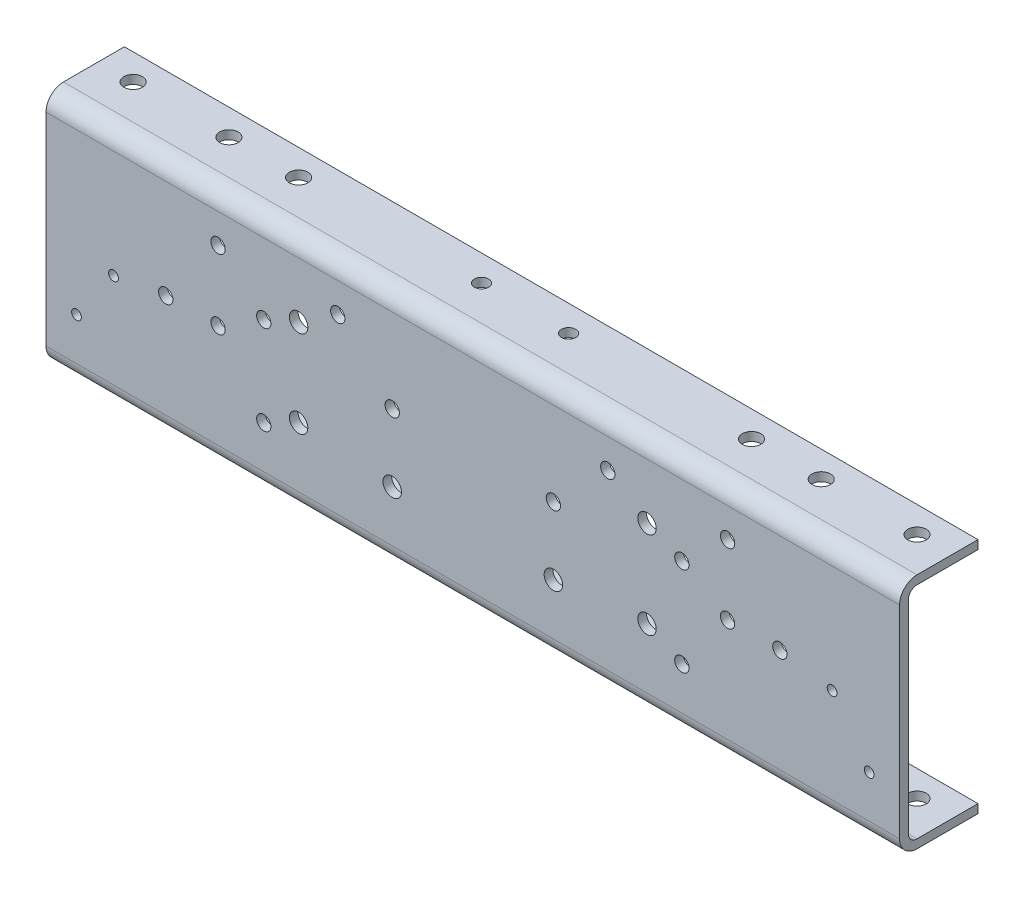
SolidWorks part; units mm, degrees
material "ASTM A36"
ref_plane "Front" through (0, 0, 0) normal (0, 0, 1) x (1, 0, 0)
ref_plane "Top" through (0, 0, 0) normal (0, 1, 0) x (1, 0, 0)
ref_plane "Side" through (0, 0, 0) normal (1, 0, 0) x (0, 0, -1)
sketch "Sketch1" plane through (0, 0, 0) normal (1, 0, 0) x (0, 0, -1)
  line L0 (57.15, 86.5188) -> (12.7, 86.5188)
  line L1 (0, 73.8188) -> (0, -73.8188)
  line L2 (12.7, -86.5187) -> (57.15, -86.5187)
  line L3 (57.15, -86.5187) -> (57.15, -80.1688)
  line L4 (57.15, -80.1688) -> (12.7, -80.1688)
  line L5 (6.35, -73.8188) -> (6.35, 73.8188)
  line L6 (12.7, 80.1688) -> (57.15, 80.1688)
  line L7 (57.15, 80.1688) -> (57.15, 86.5188)
  arc A0 (12.7, 86.5188) -> (0, 73.8188) centre (12.7, 73.8188) ccw
  arc A1 (0, -73.8188) -> (12.7, -86.5187) centre (12.7, -73.8188) ccw
  arc A2 (12.7, -80.1688) -> (6.35, -73.8188) centre (12.7, -73.8188) cw
  arc A3 (6.35, 73.8188) -> (12.7, 80.1688) centre (12.7, 73.8188) cw
  dimension "D4" = 6.35
  dimension "D1" = 6.35
  dimension "D2" = 57.15
  dimension "D3" = 173.0375
extrude "Extrude1" add sketch "Sketch1" along normal mid plane 622.3
sketch "Sketch2" plane through (0, 0, 0) normal (0, 0, 1) x (1, 0, 0)
  line L0 (0, 62.5223) -> (0, -87.3125) construction
  line L1 (58.7375, -36.5125) -> (58.7375, 12.7) construction
  line L5 (127, -30.1625) -> (127, 33.3375) construction
  line L11 (152.4, -42.8625) -> (152.4, 22.225) construction
  line L12 (288.925, -42.8625) -> (152.4, -42.8625) construction
  line L17 (185.7375, 1.5875) -> (185.7375, 52.3875) construction
  line L18 (185.7375, 52.3875) -> (98.425, 52.3875) construction
  line L20 (50, 0) -> (-50, 0) construction
  line L25 (0, -50) -> (0, 50) construction
  circle A0 centre (-152.4, 22.225) radius 5.207
  circle A1 centre (-185.7375, 52.3875) radius 5.207
  circle A2 centre (-223.8375, 1.5875) radius 5.207
  circle A3 centre (-261.9375, -4.7625) radius 3.556
  circle A4 centre (-288.925, -42.8625) radius 3.556
  circle A5 centre (-152.4, -42.8625) radius 5.207
  circle A6 centre (-127, -30.1625) radius 6.731
  circle A7 centre (-127, 33.3375) radius 6.731
  circle A8 centre (-98.425, 52.3875) radius 5.207
  circle A9 centre (-58.7375, 12.7) radius 5.207
  circle A10 centre (-58.7375, -36.5125) radius 6.731
  circle A11 centre (-185.7375, 1.5875) radius 5.207
  circle A36 centre (98.425, 52.3875) radius 5.207
  circle A37 centre (127, 33.3375) radius 6.731
  circle A38 centre (152.4, 22.225) radius 5.207
  circle A39 centre (185.7375, 52.3875) radius 5.207
  circle A40 centre (223.8375, 1.5875) radius 5.207
  circle A41 centre (185.7375, 1.5875) radius 5.207
  circle A42 centre (261.9375, -4.7625) radius 3.556
  circle A43 centre (288.925, -42.8625) radius 3.556
  circle A44 centre (152.4, -42.8625) radius 5.207
  circle A45 centre (127, -30.1625) radius 6.731
  circle A46 centre (58.7375, 12.7) radius 5.207
  circle A47 centre (58.7375, -36.5125) radius 6.731
  point P3 (0, -87.3125)
other "AlignGroup4" parameters "D25"=7.112, "D26"=10.414, "D27"=13.462, "D30"=7.112, "D17"=13.462, "D18"=10.414, "D19"=7.112, "D20"=10.414, "D21"=7.112, "D14"=10.414, "D15"=7.112, "D22"=13.462, "D23"=13.462, "D24"=13.462, "D1"=0, "D2"=61.9125, "D3"=52.3875, "D4"=12.7, "D5"=1.5875, "D6"=12.7, "D7"=52.3875, "D8"=0, "D9"=58.7375, "D10"=98.425, "D11"=127, "D12"=152.4, "D13"=185.7375, "D16"=288.925, "D28"=36.5125, "D29"=12.7, "D31"=31.75, "D32"=88.9, "D33"=139.7
extrude "Cut-Web Holes" cut sketch "Sketch2" against normal through all
sketch "Sketch3" plane through (0, 0, 0) normal (0, 1, 0) x (1, 0, 0)
  line L0 (-165.1, 38.1) -> (-31.75, 38.1) construction
  line L1 (-31.75, 38.1) -> (31.75, 38.1) construction
  line L2 (31.75, 38.1) -> (165.1, 38.1) construction
  line L3 (-50, 0) -> (50, 0) construction
  line L4 (0, -50) -> (0, 50) construction
  line L5 (-311.15, 57.15) -> (-311.15, 12.7) construction
  line L7 (-215.9, 38.1) -> (-285.75, 38.1) construction
  line L8 (0, 0) -> (0, 40.7701) construction
  circle A0 centre (-285.75, 38.1) radius 6.731
  circle A1 centre (-215.9, 38.1) radius 6.731
  circle A2 centre (285.75, 38.1) radius 6.731
  circle A3 centre (215.9, 38.1) radius 6.731
  circle A4 centre (165.1, 38.1) radius 6.731
  circle A5 centre (31.75, 38.1) radius 5.207
  circle A6 centre (-31.75, 38.1) radius 5.207
  circle A7 centre (-165.1, 38.1) radius 6.731
other "AlignGroup1" parameters "D7"=10.414, "D8"=13.462, "D1"=100, "D2"=0, "D3"=31.75, "D4"=165.1, "D5"=31.75, "D6"=165.1, "D9"=311.15, "D10"=215.9, "D11"=285.75, "D12"=100
extrude "Cut-Flg Holes" cut sketch "Sketch3" along normal through all and the other way through all
